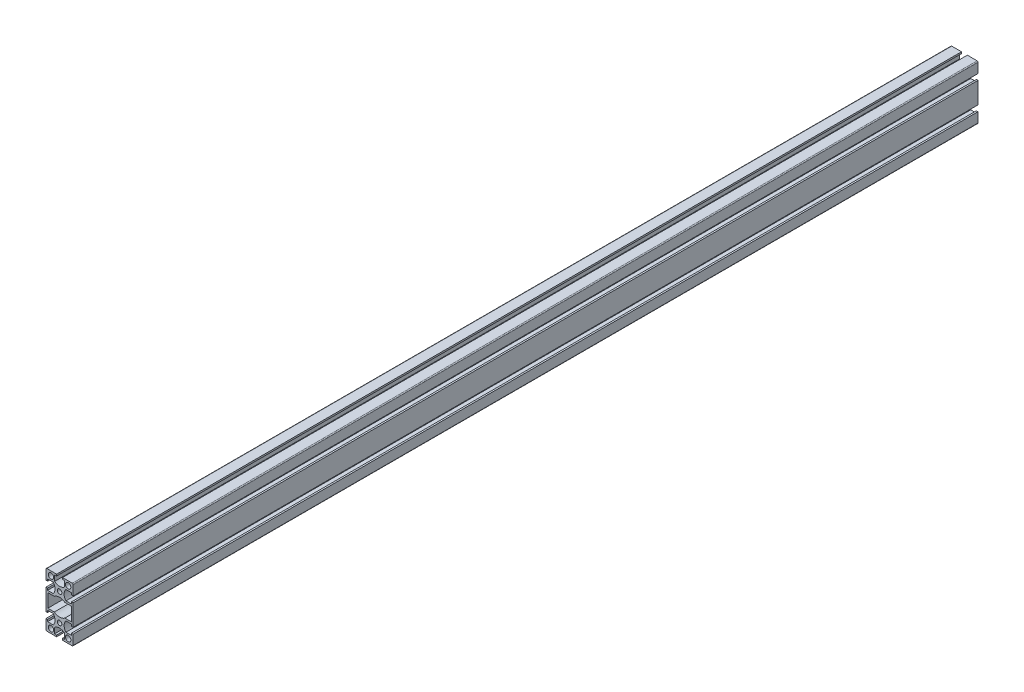
SolidWorks part; units mm, degrees
material "6063 T5"
ref_plane "Спереди" through (0, 0, 0) normal (0, 0, 1) x (1, 0, 0)
ref_plane "Сверху" through (0, 0, 0) normal (0, 1, 0) x (1, 0, 0)
ref_plane "Справа" through (0, 0, 0) normal (1, 0, 0) x (0, 0, -1)
sketch "Эскиз1" plane through (0, 0, 0) normal (0, 0, 1) x (1, 0, 0)
  line L0 (-15, 0) -> (15, 0) construction
  line L1 (0, 0) -> (0, -30) construction
  line L2 (0, -15) -> (-19.5523, -15) construction
  line L3 (-15, -30) -> (15, -30) construction
  line L4 (-15, 5.45) -> (-15, 14)
  line L5 (-14, 15) -> (-5.45, 15)
  line L6 (5.45, 15) -> (14, 15)
  line L7 (15, 14) -> (15, 5.45)
  line L8 (15, -5.45) -> (15, -24.55)
  line L9 (-15.5211, 15.0233) -> (-15.5211, -44.9767) construction
  line L10 (15, -35.45) -> (15, -44)
  line L11 (14, -45) -> (5.45, -45)
  line L12 (-5.45, -45) -> (-14, -45)
  line L13 (-15, -44) -> (-15, -35.45)
  line L14 (-15, -24.55) -> (-15, -5.45)
  line L15 (-13, -22.5) -> (-13, -7.5)
  line L16 (9.5, -40.25) -> (-9.5, -40.25) construction
  line L17 (9.5, -40.25) -> (9.5, 10.25) construction
  line L18 (9.5, 10.25) -> (-9.5, 10.25) construction
  line L19 (-9.5, -40.25) -> (-9.5, 10.25) construction
  line L20 (9.5, -40.25) -> (-9.5, 10.25) construction
  line L21 (9.5, 10.25) -> (-9.5, -40.25) construction
  line L22 (-13, -7.5) -> (-5.831, -7.5)
  line L23 (13, -22.5) -> (13, -7.5)
  line L24 (13, -7.5) -> (5.831, -7.5)
  line L25 (13, -22.5) -> (5.831, -22.5)
  line L26 (-13, -22.5) -> (-5.831, -22.5)
  line L27 (-22.7162, 15.0508) -> (-22.7162, -44.9492) construction
  circle A0 centre (0, 0) radius 2.5
  circle A1 centre (0, -30) radius 2.5
  circle A2 centre (-9.5, 10.25) radius 3
  circle A3 centre (9.5, 10.25) radius 3
  circle A4 centre (-9.5, -40.25) radius 3
  circle A5 centre (9.5, -40.25) radius 3
  arc A6 (-5.831, -7.5) -> (5.831, -7.5) centre (0, -15) cw
  arc A7 (-5.831, -22.5) -> (5.831, -22.5) centre (0, -15) ccw
  arc A8 (15, -44) -> (14, -45) centre (14, -44) cw
  arc A9 (-14, -45) -> (-15, -44) centre (-14, -44) cw
  arc A10 (14, 15) -> (15, 14) centre (14, 14) cw
  arc A11 (-15, 14) -> (-14, 15) centre (-14, 14) cw
  point P2 (0, 0)
  point P10 (0, -30)
  point P55 (13, -15)
  point P56 (-13, -15)
  line B0 (-15, 5.45) -> (-15, 3.25)
  line B1 (-15, 3.25) -> (-13.2, 3.25)
  line B2 (-13.2, 3.25) -> (-13.2, 5.45)
  line B3 (-13.2, 5.45) -> (-7, 5.45)
  line B4 (-7, -5.45) -> (-13.2, -5.45)
  line B5 (-13.2, -5.45) -> (-13.2, -3.25)
  line B6 (-13.2, -3.25) -> (-15, -3.25)
  line B7 (-15, -3.25) -> (-15, -5.45)
  line B8 (-15, 5.45) -> (-15, -5.45) construction
  arc B9 (-7, 5.45) -> (-7, -5.45) centre (-13.5228, 0) cw
  line B10 (5.45, 15) -> (3.25, 15)
  line B11 (3.25, 15) -> (3.25, 13.2)
  line B12 (3.25, 13.2) -> (5.45, 13.2)
  line B13 (5.45, 13.2) -> (5.45, 7)
  line B14 (-5.45, 7) -> (-5.45, 13.2)
  line B15 (-5.45, 13.2) -> (-3.25, 13.2)
  line B16 (-3.25, 13.2) -> (-3.25, 15)
  line B17 (-3.25, 15) -> (-5.45, 15)
  line B18 (5.45, 15) -> (-5.45, 15) construction
  arc B19 (5.45, 7) -> (-5.45, 7) centre (0, 13.5228) cw
  line B20 (15, -5.45) -> (15, -3.25)
  line B21 (15, -3.25) -> (13.2, -3.25)
  line B22 (13.2, -3.25) -> (13.2, -5.45)
  line B23 (13.2, -5.45) -> (7, -5.45)
  line B24 (7, 5.45) -> (13.2, 5.45)
  line B25 (13.2, 5.45) -> (13.2, 3.25)
  line B26 (13.2, 3.25) -> (15, 3.25)
  line B27 (15, 3.25) -> (15, 5.45)
  line B28 (15, -5.45) -> (15, 5.45) construction
  arc B29 (7, -5.45) -> (7, 5.45) centre (13.5228, 0) cw
  line B30 (-15, -35.45) -> (-15, -33.25)
  line B31 (-15, -33.25) -> (-13.2, -33.25)
  line B32 (-13.2, -33.25) -> (-13.2, -35.45)
  line B33 (-13.2, -35.45) -> (-7, -35.45)
  line B34 (-7, -24.55) -> (-13.2, -24.55)
  line B35 (-13.2, -24.55) -> (-13.2, -26.75)
  line B36 (-13.2, -26.75) -> (-15, -26.75)
  line B37 (-15, -26.75) -> (-15, -24.55)
  line B38 (-15, -35.45) -> (-15, -24.55) construction
  arc B39 (-7, -35.45) -> (-7, -24.55) centre (-13.5228, -30) ccw
  line B40 (5.45, -45) -> (3.25, -45)
  line B41 (3.25, -45) -> (3.25, -43.2)
  line B42 (3.25, -43.2) -> (5.45, -43.2)
  line B43 (5.45, -43.2) -> (5.45, -37)
  line B44 (-5.45, -37) -> (-5.45, -43.2)
  line B45 (-5.45, -43.2) -> (-3.25, -43.2)
  line B46 (-3.25, -43.2) -> (-3.25, -45)
  line B47 (-3.25, -45) -> (-5.45, -45)
  line B48 (5.45, -45) -> (-5.45, -45) construction
  arc B49 (5.45, -37) -> (-5.45, -37) centre (0, -43.5228) ccw
  line B50 (15, -24.55) -> (15, -26.75)
  line B51 (15, -26.75) -> (13.2, -26.75)
  line B52 (13.2, -26.75) -> (13.2, -24.55)
  line B53 (13.2, -24.55) -> (7, -24.55)
  line B54 (7, -35.45) -> (13.2, -35.45)
  line B55 (13.2, -35.45) -> (13.2, -33.25)
  line B56 (13.2, -33.25) -> (15, -33.25)
  line B57 (15, -33.25) -> (15, -35.45)
  line B58 (15, -24.55) -> (15, -35.45) construction
  arc B59 (7, -24.55) -> (7, -35.45) centre (13.5228, -30) ccw
  dimension "D4" = 6
  dimension "D3" = 5
  dimension "D8" = 9.5
  dimension "D11" = 1
  dimension "D1" = 30
  dimension "D2" = 30
  dimension "D5" = 19
  dimension "D6" = 60
  dimension "D7" = 50.5
  dimension "D9" = 7.5
  dimension "D10" = 26
  dimension "D12" = 60
sketch_block_instance "Блок1-1"
sketch_block "Блок1" parameters "D5"=8.5, "D1"=10.9, "D2"=6.5, "D3"=1.8, "D4"=6.2
sketch_block_instance "Блок1-2"
sketch_block_instance "Блок1-3"
sketch_block_instance "Блок1-4"
sketch_block_instance "Блок1-5"
sketch_block_instance "Блок1-6"
extrude "Бобышка-Вытянуть1" add sketch "Эскиз1" along normal blind 1000 contours B59 B53 B52 B51 B50 L8 B20 B21 B22 B23 B29 B24 B25 B26 B27 L7 A10 L6 B10 B11 B12 B13 B19 B14 B15 B16 B17 L5 A11 L4 B0 B1 B2 B3 B9 B4 B5 B6 B7 L14 B37 B36 B35 B34 B39 B33 B32 B31 B30 L13 A9
